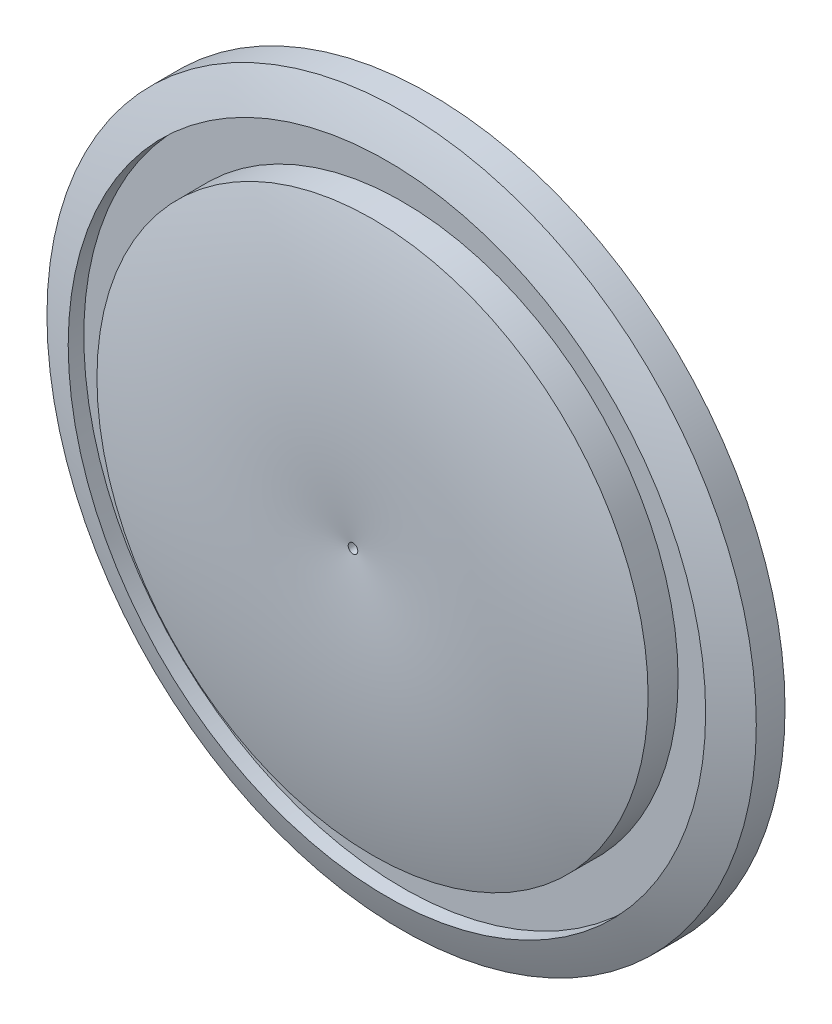
SolidWorks part; units mm, degrees
ref_plane "Front Plane" through (0, 0, 0) normal (0, 0, 1) x (1, 0, 0)
ref_plane "Top Plane" through (0, 0, 0) normal (0, 1, 0) x (1, 0, 0)
ref_plane "Right Plane" through (0, 0, 0) normal (1, 0, 0) x (0, 0, -1)
sketch "Sketch1" plane through (0, 0, 0) normal (0, 1, 0) x (1, 0, 0)
  line L0 (0, 18.5246) -> (0, -13.7108) construction
  line L1 (0, 2.4069) -> (-37, 2.4069)
  line L2 (-37, 2.4069) -> (-37, -0.5931)
  line L3 (0, 2.4069) -> (0, -5.5931)
  arc A0 (-37, -0.5931) -> (0, -5.5931) centre (-9.942, 60.2364) ccw
  dimension "D1" = 37
  dimension "D2" = 3
  dimension "D3" = 8
revolve "Revolve1" add sketch "Sketch1" angle 360 about L0
sketch "Sketch2" plane through (0, 0, -2.4069) normal (0, 0, -1) x (-1, 0, 0)
  circle A0 centre (0, 0) radius 0.5
  dimension "D1" = 1
extrude "Cut-Extrude1" cut sketch "Sketch2" against normal through all
ref_plane "Plane1" through (0, 0, 8) normal (0, 0, 1) x (1, 0, 0)
sketch "Sketch3" plane through (0, 0, 8) normal (0, 0, 1) x (1, 0, 0)
  circle A0 centre (0, 0) radius 33.25
  circle A1 centre (0, 0) radius 28.75
  dimension "D1" = 66.5
  dimension "D2" = 57.5
extrude "Cut-Extrude3" cut sketch "Sketch3" against normal blind 7.5
